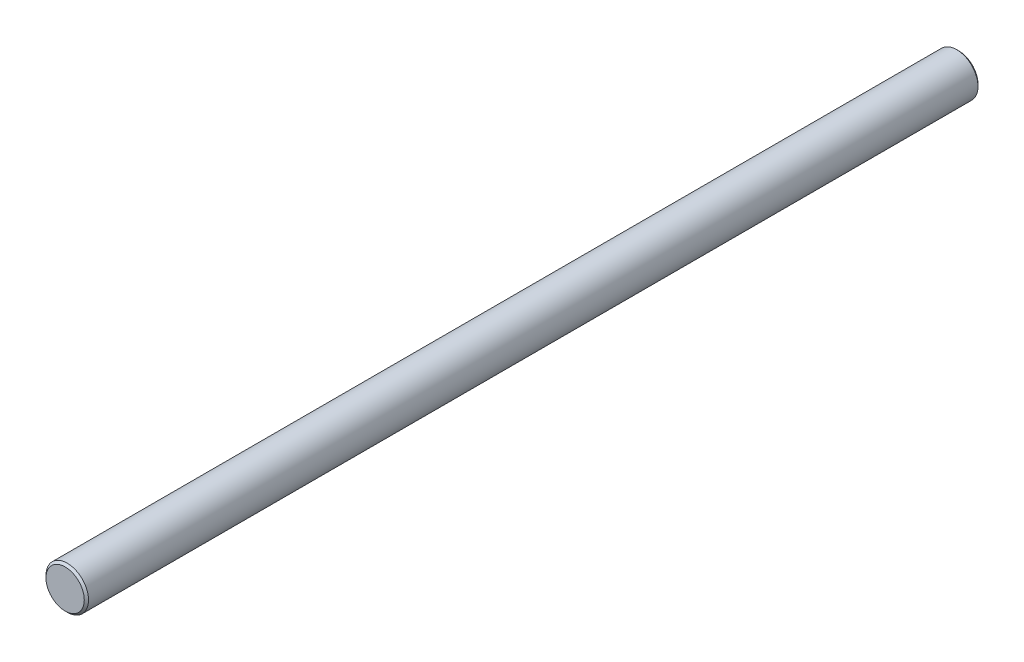
SolidWorks part; units mm, degrees
material "AISI 304"
ref_plane "Front Plane" through (0, 0, 0) normal (0, 0, 1) x (1, 0, 0)
ref_plane "Top Plane" through (0, 0, 0) normal (0, 1, 0) x (1, 0, 0)
ref_plane "Right Plane" through (0, 0, 0) normal (1, 0, 0) x (0, 0, -1)
sketch "Sketch1" plane through (0, 0, 0) normal (0, 0, 1) x (1, 0, 0)
  circle A0 centre (0, 0) radius 5
  dimension "D1" = 10
extrude "Boss-Extrude1" add sketch "Sketch1" against normal blind 210
cosmetic thread "Cosmetic Thread1" parameters "D2"=6.619
chamfer "Chamfer1" distance 0.5 angle 45 2 edges at (5, 0, -210) (5, 0, 0)
